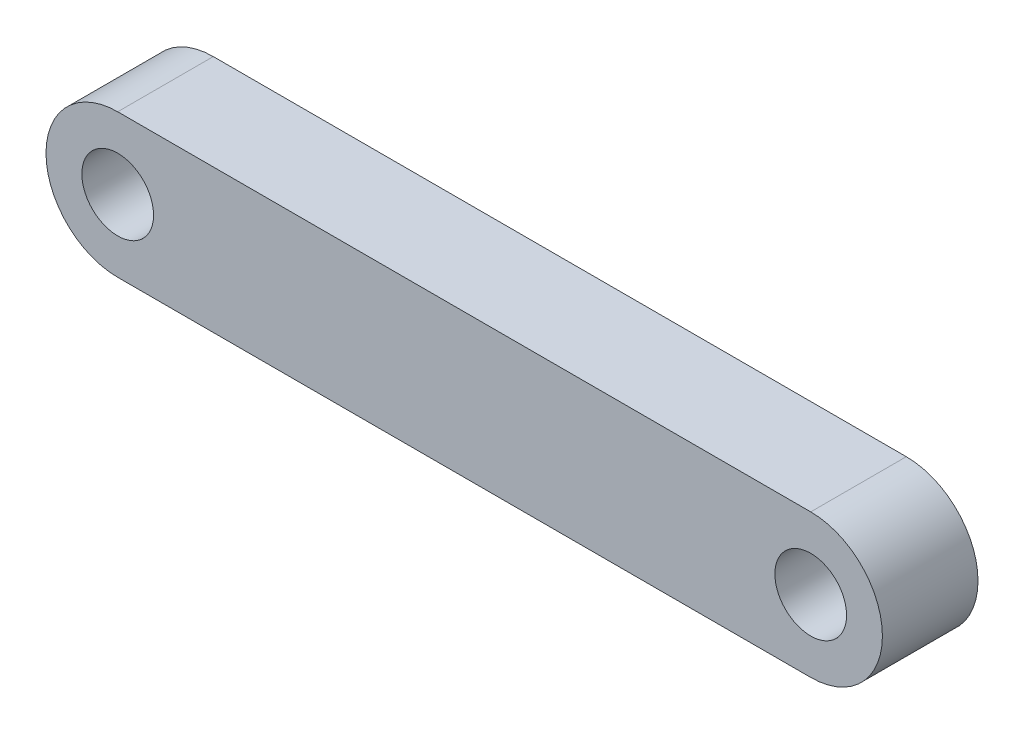
SolidWorks part; units mm, degrees
material "Beech"
ref_plane "Front Plane" through (0, 0, 0) normal (0, 0, 1) x (1, 0, 0)
ref_plane "Top Plane" through (0, 0, 0) normal (0, 1, 0) x (1, 0, 0)
ref_plane "Right Plane" through (0, 0, 0) normal (1, 0, 0) x (0, 0, -1)
sketch "Sketch1" plane through (0, 0, 0) normal (0, 0, 1) x (1, 0, 0)
  line L0 (3, 6) -> (32, 6)
  line L1 (32, 0) -> (3, 0)
  arc A0 (3, 6) -> (3, 0) centre (3, 3) ccw
  arc A1 (32, 0) -> (32, 6) centre (32, 3) ccw
  circle A2 centre (3, 3) radius 1.5
  circle A3 centre (32, 3) radius 1.5
extrude "Boss-Extrude1" add sketch "Sketch1" along normal blind 4
